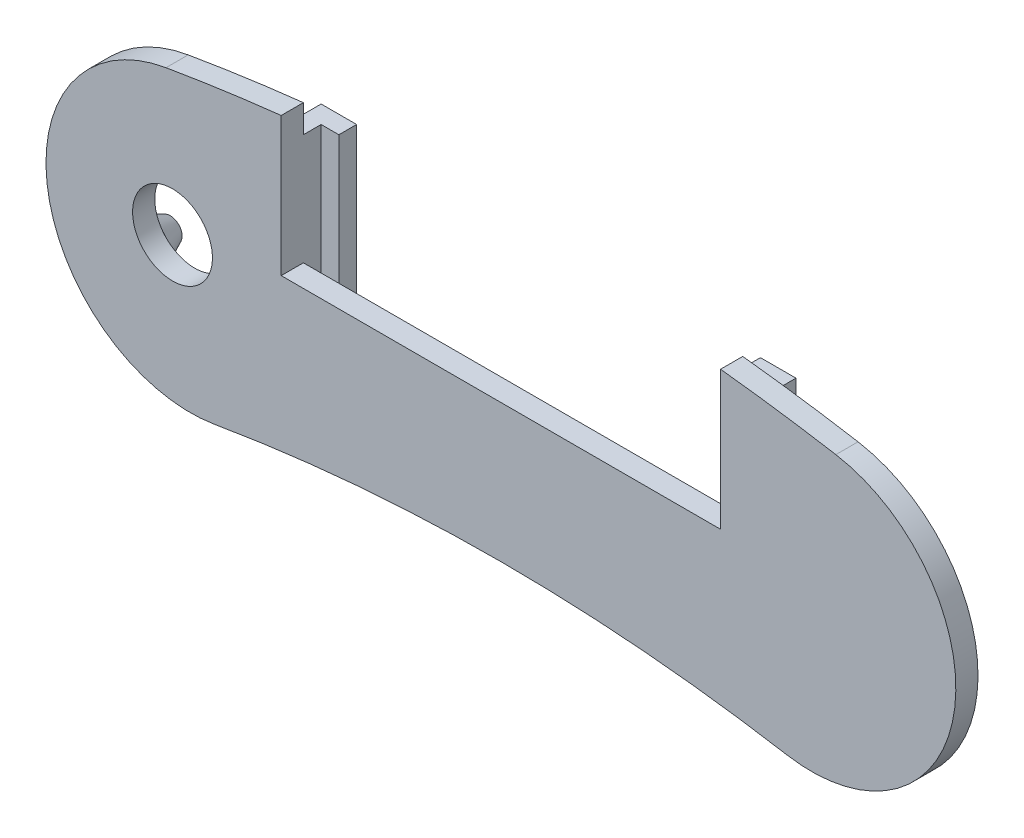
SolidWorks part; units mm, degrees
ref_plane "Plan de face" through (0, 0, 0) normal (0, 0, 1) x (1, 0, 0)
ref_plane "Plan de dessus" through (0, 0, 0) normal (0, 1, 0) x (1, 0, 0)
ref_plane "Plan de droite" through (0, 0, 0) normal (1, 0, 0) x (0, 0, -1)
sketch "Esquisse3" plane through (0, 0, 0) normal (0, 0, 1) x (1, 0, 0)
  arc A0 (-69.9014, 409.0706) -> (70.0986, 409.0369) centre (0, 0) cw construction
  arc A1 (75.5942, 441.1049) -> (-75.3816, 441.1413) centre (0, 0) ccw
  arc A2 (64.6029, 376.9689) -> (-64.4212, 377) centre (0, 0) ccw
  arc A3 (64.6029, 376.9689) -> (75.5942, 441.1049) centre (70.0986, 409.0369) ccw
  arc A4 (-75.3816, 441.1413) -> (-64.4212, 377) centre (-69.9014, 409.0706) ccw
  point P4 (0.1, 415)
  dimension "D1" = 415
  dimension "D4" = 38
  dimension "D2" = 140
  dimension "D3" = 0.1
extrude "Boss.-Extru.1" add sketch "Esquisse3" along normal blind 5
sketch "Esquisse14" plane through (0, 0, 0) normal (0, 0, -1) x (-1, 0, 0)
  line L1 (49.4212, 413.5355) -> (-49.6029, 413.5355)
  line L2 (49.4212, 413.5355) -> (49.4212, 447.5355)
  line L3 (49.4212, 447.5355) -> (-49.6029, 447.5355)
  line L4 (-49.6029, 413.5355) -> (-49.6029, 447.5355)
  arc A0 (75.3816, 441.1413) -> (-75.5942, 441.1049) centre (0, 0) ccw construction
  point P9 (-0.1078, 447.5355)
  dimension "D1" = 15
  dimension "D2" = 15
  dimension "D3" = 34
  dimension "D4" = 0
extrude "Enlèv. mat.-Extru.3" cut sketch "Esquisse14" against normal blind 10 contours L2 L1 L4 L3
sketch "Esquisse15" plane through (0, 0, 0) normal (0, 0, -1) x (-1, 0, 0)
  line L0 (-49.6029, 413.5355) -> (-49.6029, 444.7781) construction
  line L1 (-53.6029, 438.5355) -> (-49.6029, 438.5355)
  line L2 (-53.6029, 438.5355) -> (-53.6029, 383.5355)
  line L3 (-53.6029, 383.5355) -> (-49.6029, 383.5355)
  line L4 (-49.6029, 438.5355) -> (-49.6029, 383.5355)
  line L5 (49.4212, 413.5355) -> (-49.6029, 413.5355) construction
  line L6 (49.4212, 413.5355) -> (49.4212, 444.7984) construction
  line L7 (49.4212, 438.5355) -> (53.4212, 438.5355)
  line L8 (49.4212, 438.5355) -> (49.4212, 383.5355)
  line L9 (49.4212, 383.5355) -> (53.4212, 383.5355)
  line L10 (53.4212, 438.5355) -> (53.4212, 383.5355)
  dimension "D1" = 4
  dimension "D2" = 55
  dimension "D3" = 0
  dimension "D4" = 30
  dimension "D5" = 4
extrude "Boss.-Extru.2" add sketch "Esquisse15" along normal blind 8
sketch "Esquisse16" plane through (49.6029, 0, 0) normal (-1, 0, 0) x (0, 0, 1)
  line L0 (-8, 383.5355) -> (-8, 438.5355) construction
  line L1 (-8, 438.5355) -> (-4, 438.5355)
  line L2 (-8, 438.5355) -> (-8, 383.5355)
  line L3 (-8, 383.5355) -> (-4, 383.5355)
  line L4 (-4, 438.5355) -> (-4, 383.5355)
  line L5 (-8, 438.5355) -> (0, 438.5355) construction
  line L6 (-8, 383.5355) -> (0, 383.5355) construction
  dimension "D1" = 0
  dimension "D2" = 4
  dimension "D3" = 0
  dimension "D4" = 0
extrude "Boss.-Extru.3" add sketch "Esquisse16" along normal blind 4
sketch "Esquisse17" plane through (-49.4212, 0, 0) normal (1, 0, 0) x (0, 0, -1)
  line L0 (8, 438.5355) -> (8, 383.5355) construction
  line L1 (4, 383.5355) -> (8, 383.5355)
  line L2 (4, 383.5355) -> (4, 438.5355)
  line L3 (4, 438.5355) -> (8, 438.5355)
  line L4 (8, 383.5355) -> (8, 438.5355)
  line L5 (8, 383.5355) -> (0, 383.5355) construction
  line L6 (8, 438.5355) -> (0, 438.5355) construction
  dimension "D1" = 0
  dimension "D2" = 0
  dimension "D3" = 4
  dimension "D4" = 0
extrude "Boss.-Extru.4" add sketch "Esquisse17" along normal blind 4
sketch "Esquisse18" plane through (0, 0, 0) normal (0, 0, -1) x (-1, 0, 0)
  line L0 (53.4212, 383.5355) -> (53.4212, 438.5355) construction
  circle A0 centre (63.4212, 400.0706) radius 5
  circle A1 centre (84.4212, 400.0706) radius 5
  circle A2 centre (73.9212, 429.2383) radius 5
  arc A3 (64.4212, 377) -> (75.3816, 441.1413) centre (69.9014, 409.0706) ccw construction
  point P10 (94.2426, 336.4743)
  dimension "D1" = 10
  dimension "D2" = 21
  dimension "D3" = 31
  dimension "D4" = 31
  dimension "D5" = 0
  dimension "D6" = 9
extrude "Boss.-Extru.5" add sketch "Esquisse18" along normal blind 5 draft 25
sketch "Esquisse19" plane through (0, 0, 0) normal (0, 0, -1) x (-1, 0, 0)
  circle A0 centre (73.9212, 409.2383) radius 9
  circle A1 centre (73.9212, 429.2383) radius 2.6685 construction
  circle A2 centre (63.4212, 400.0706) radius 2.6685 construction
  dimension "D1" = 20
  dimension "D2" = 10.5
extrude "Enlèv. mat.-Extru.4" cut sketch "Esquisse19" against normal blind 5
